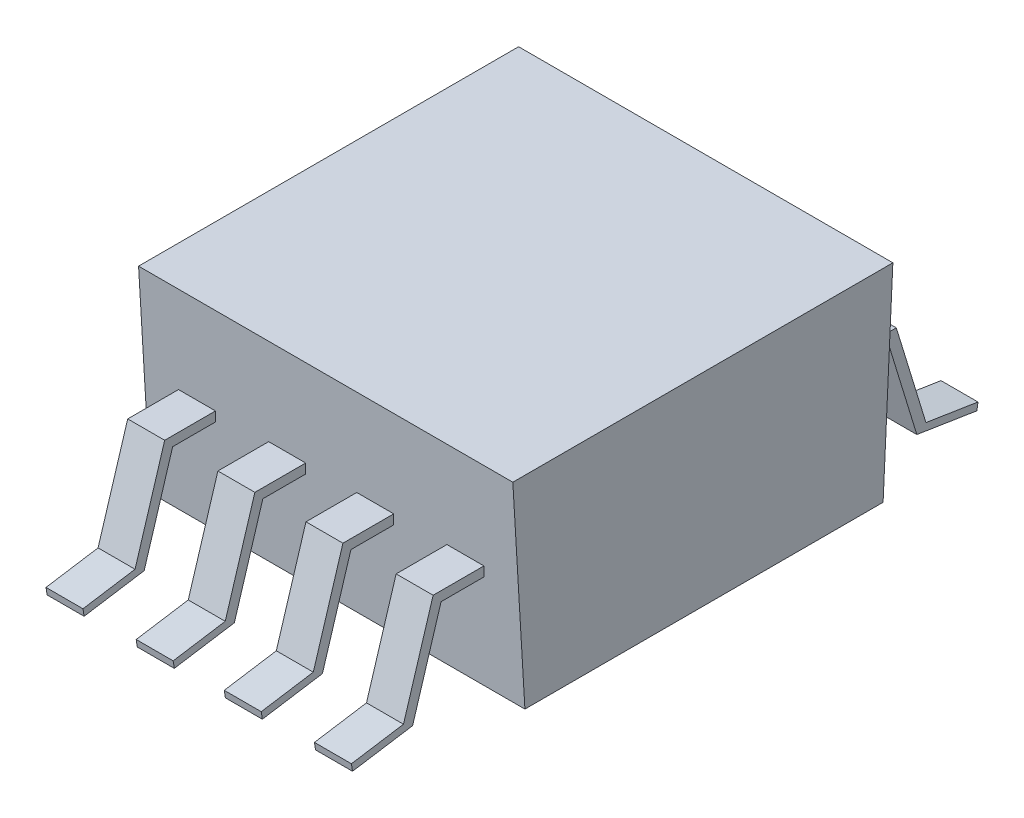
SolidWorks part; units mm, degrees
ref_plane "Front Plane" through (0, 0, 0) normal (0, 0, 1) x (1, 0, 0)
ref_plane "Top Plane" through (0, 0, 0) normal (0, 1, 0) x (1, 0, 0)
ref_plane "Right Plane" through (0, 0, 0) normal (1, 0, 0) x (0, 0, -1)
sketch "Sketch1" plane through (0, 0, 0) normal (1, 0, 0) x (0, 0, -1)
  line L0 (-1.5875, 13.208) -> (-1.5875, 6.731)
  line L1 (-1.5875, 6.731) -> (-5.5149, 6.731)
  line L2 (-5.5149, 6.731) -> (-5.5149, 4.2035)
  line L3 (-5.5149, 4.2035) -> (-5.2758, 4.2035)
  line L4 (-5.2758, 4.2035) -> (-5.0251, 0)
  line L5 (-5.0251, 0) -> (5.306, 0)
  line L6 (5.306, 0) -> (5.5132, 4.2942)
  line L7 (5.5132, 4.2942) -> (5.824, 4.2942)
  line L8 (5.824, 4.2942) -> (5.824, 6.731)
  line L9 (5.824, 6.731) -> (1.5875, 6.731)
  line L10 (1.5875, 6.731) -> (1.5875, 13.208)
  line L11 (1.5875, 13.208) -> (-1.5875, 13.208)
  line L12 (0, 13.208) -> (0, 0) construction
  line L13 (-4.8797, 2.8996) -> (-6.45, 2.8996)
  line L14 (-6.45, 2.8996) -> (-7.2719, 0.2127)
  line L15 (-7.2719, 0.2127) -> (-9.004, -0.0601)
  line L16 (-9.004, -0.0601) -> (-9.0362, 0.1445)
  line L17 (-9.0362, 0.1445) -> (-7.5346, 0.3811)
  line L18 (-7.5346, 0.3811) -> (-6.6798, 3.1753)
  line L19 (-6.6798, 3.1753) -> (-4.8793, 3.1753)
  dimension "D1" = 3.175
  dimension "D2" = 6.477
  dimension "D3" = 13.208
sketch "Sketch4" plane through (0, 0, 0) normal (1, 0, 0) x (0, 0, -1)
  line L0 (-4.8797, 2.8996) -> (-6.45, 2.8996) construction
  line L1 (-6.45, 2.8996) -> (-7.2719, 0.2127) construction
  line L2 (-7.2719, 0.2127) -> (-9.004, -0.0601) construction
  line L3 (-9.004, -0.0601) -> (-9.0362, 0.1445) construction
  line L4 (-9.0362, 0.1445) -> (-7.5346, 0.3811) construction
  line L5 (-7.5346, 0.3811) -> (-6.6798, 3.1753) construction
  line L6 (-6.6798, 3.1753) -> (-4.8793, 3.1753) construction
  line L7 (-5.198, 2.8996) -> (-6.45, 2.8996)
  line L8 (-6.45, 2.8996) -> (-7.2719, 0.2127)
  line L9 (-7.2719, 0.2127) -> (-9.004, -0.0601)
  line L10 (-9.004, -0.0601) -> (-9.0362, 0.1445)
  line L11 (-9.0362, 0.1445) -> (-7.5346, 0.3811)
  line L12 (-7.5346, 0.3811) -> (-6.6798, 3.1753)
  line L13 (-6.6798, 3.1753) -> (-5.2145, 3.1753)
  line L14 (-5.2758, 4.2035) -> (-5.0251, 0) construction
  line L15 (-5.2145, 3.1753) -> (-5.198, 2.8996)
  line L16 (0, 13.208) -> (0, 0) construction
  line L17 (0, 13.208) -> (0, 0) construction
  line L18 (5.2145, 3.1753) -> (5.198, 2.8996)
  line L19 (6.6798, 3.1753) -> (5.2145, 3.1753)
  line L20 (7.5346, 0.3811) -> (6.6798, 3.1753)
  line L21 (9.0362, 0.1445) -> (7.5346, 0.3811)
  line L22 (9.004, -0.0601) -> (9.0362, 0.1445)
  line L23 (7.2719, 0.2127) -> (9.004, -0.0601)
  line L24 (6.45, 2.8996) -> (7.2719, 0.2127)
  line L25 (5.198, 2.8996) -> (6.45, 2.8996)
extrude "Extrude2" add sketch "Sketch4" along normal mid plane 10.795
sketch "Sketch5" plane through (0, 3.1753, 0) normal (0, 1, 0) x (1, 0, 0)
  line L0 (0, -5.0251) -> (0, 5.306) construction
  line L1 (-4.4046, -5.2145) -> (-3.3378, -5.2145)
  line L2 (-4.4046, -5.2145) -> (-4.4046, -9.0362)
  line L3 (-4.4046, -9.0362) -> (-3.3378, -9.0362)
  line L4 (-3.3378, -5.2145) -> (-3.3378, -9.0362)
  line L5 (-1.8034, -5.2145) -> (-0.7366, -5.2145)
  line L6 (-1.8034, -5.2145) -> (-1.8034, -9.0362)
  line L7 (-1.8034, -9.0362) -> (-0.7366, -9.0362)
  line L8 (-0.7366, -5.2145) -> (-0.7366, -9.0362)
  line L9 (0, -5.0251) -> (0, 5.306) construction
  line L10 (0, 0) -> (-10.3312, 0) construction
  line L11 (5.3975, -5.2145) -> (-5.3975, -5.2145) construction
  line L12 (5.3975, -9.0362) -> (-5.3975, -9.0362) construction
  line L13 (4.4046, -5.2145) -> (3.3378, -5.2145)
  line L14 (4.4046, -5.2145) -> (4.4046, -9.0362)
  line L15 (4.4046, -9.0362) -> (3.3378, -9.0362)
  line L16 (3.3378, -5.2145) -> (3.3378, -9.0362)
  line L17 (1.8034, -5.2145) -> (0.7366, -5.2145)
  line L18 (1.8034, -5.2145) -> (1.8034, -9.0362)
  line L19 (1.8034, -9.0362) -> (0.7366, -9.0362)
  line L20 (0.7366, -5.2145) -> (0.7366, -9.0362)
  line L21 (-4.4046, 5.2145) -> (-3.3378, 5.2145)
  line L22 (-4.4046, 5.2145) -> (-4.4046, 9.0362)
  line L23 (-4.4046, 9.0362) -> (-3.3378, 9.0362)
  line L24 (-3.3378, 5.2145) -> (-3.3378, 9.0362)
  line L25 (-1.8034, 5.2145) -> (-0.7366, 5.2145)
  line L26 (-1.8034, 5.2145) -> (-1.8034, 9.0362)
  line L27 (-1.8034, 9.0362) -> (-0.7366, 9.0362)
  line L28 (-0.7366, 5.2145) -> (-0.7366, 9.0362)
  line L29 (1.8034, 5.2145) -> (0.7366, 5.2145)
  line L30 (0.7366, 5.2145) -> (0.7366, 9.0362)
  line L31 (1.8034, 9.0362) -> (0.7366, 9.0362)
  line L32 (1.8034, 5.2145) -> (1.8034, 9.0362)
  line L33 (4.4046, 5.2145) -> (3.3378, 5.2145)
  line L34 (3.3378, 5.2145) -> (3.3378, 9.0362)
  line L35 (4.4046, 9.0362) -> (3.3378, 9.0362)
  line L36 (4.4046, 5.2145) -> (4.4046, 9.0362)
  point P17 (-1.27, -9.0362)
  point P18 (-3.8712, -9.0362)
  dimension "D1" = 2.6012
  dimension "D2" = 1.27
  dimension "D3" = 1.0668
extrude "Extrude3" cut sketch "Sketch5" against normal through all flip side to cut
sketch "Sketch2" plane through (0, 0, 0) normal (1, 0, 0) x (0, 0, -1)
  line L26 (-1.5875, 13.208) -> (-1.5875, 6.731)
  line L27 (-1.5875, 6.731) -> (-5.5149, 6.731)
  line L28 (-5.5149, 6.731) -> (-5.5149, 4.2035)
  line L29 (-5.5149, 4.2035) -> (-5.2758, 4.2035)
  line L30 (-5.2758, 4.2035) -> (-5.0251, 0)
  line L31 (-5.0251, 0) -> (5.306, 0)
  line L32 (5.306, 0) -> (5.5132, 4.2942)
  line L33 (5.5132, 4.2942) -> (5.824, 4.2942)
  line L34 (5.824, 4.2942) -> (5.824, 6.731)
  line L35 (5.824, 6.731) -> (1.5875, 6.731)
  line L36 (1.5875, 6.731) -> (1.5875, 13.208)
  line L37 (1.5875, 13.208) -> (-1.5875, 13.208)
  line L41 (5.5879, 5.842) -> (-5.3735, 5.842)
  line L42 (-5.3735, 5.842) -> (-5.0251, 0)
  line L43 (-5.0251, 0) -> (5.306, 0)
  line L44 (5.306, 0) -> (5.5879, 5.842)
  dimension "D2" = 5.842
  dimension "D1" = 0
extrude "Extrude1" add sketch "Sketch2" along normal mid plane 10.795 contours L42 L43 L44 L41
sketch "Sketch3" plane through (0, 0, 0) normal (1, 0, 0) x (0, 0, -1)
  line L8 (0, 13.208) -> (0, 0) construction
  line L9 (0, 13.208) -> (0, 4.2035)
  line L10 (-5.5149, 4.2035) -> (-5.2758, 4.2035) construction
  line L11 (-5.5149, 6.731) -> (-5.5149, 4.2035) construction
  line L12 (-1.5875, 6.731) -> (-5.5149, 6.731) construction
  line L13 (-5.5149, 4.2035) -> (0, 4.2035)
  line L14 (-5.5149, 6.731) -> (-5.5149, 4.2035)
  line L15 (-2.3495, 6.731) -> (-5.5149, 6.731)
  line L26 (-1.5875, 13.208) -> (-1.5875, 6.731)
  line L27 (-1.5875, 6.731) -> (-5.5149, 6.731)
  line L28 (-5.5149, 6.731) -> (-5.5149, 4.2035)
  line L29 (-5.5149, 4.2035) -> (-5.2758, 4.2035)
  line L30 (-5.2758, 4.2035) -> (-5.0251, 0)
  line L31 (-5.0251, 0) -> (5.306, 0)
  line L32 (5.306, 0) -> (5.5132, 4.2942)
  line L33 (5.5132, 4.2942) -> (5.824, 4.2942)
  line L34 (5.824, 4.2942) -> (5.824, 6.731)
  line L35 (5.824, 6.731) -> (1.5875, 6.731)
  line L36 (1.5875, 6.731) -> (1.5875, 13.208)
  line L37 (1.5875, 13.208) -> (-1.5875, 13.208)
  line L38 (-1.5875, 12.446) -> (-1.5875, 7.493)
  line L49 (0, 13.208) -> (-0.8255, 13.208)
  arc A0 (-0.8255, 13.208) -> (-1.5875, 12.446) centre (-0.8255, 12.446) ccw
  arc A3 (-2.3495, 6.731) -> (-1.5875, 7.493) centre (-2.3495, 7.493) ccw
  dimension "D2" = 0.762
  dimension "D1" = 0
revolve "Revolve1" [suppressed] add sketch "Sketch3" angle 360 about L9
